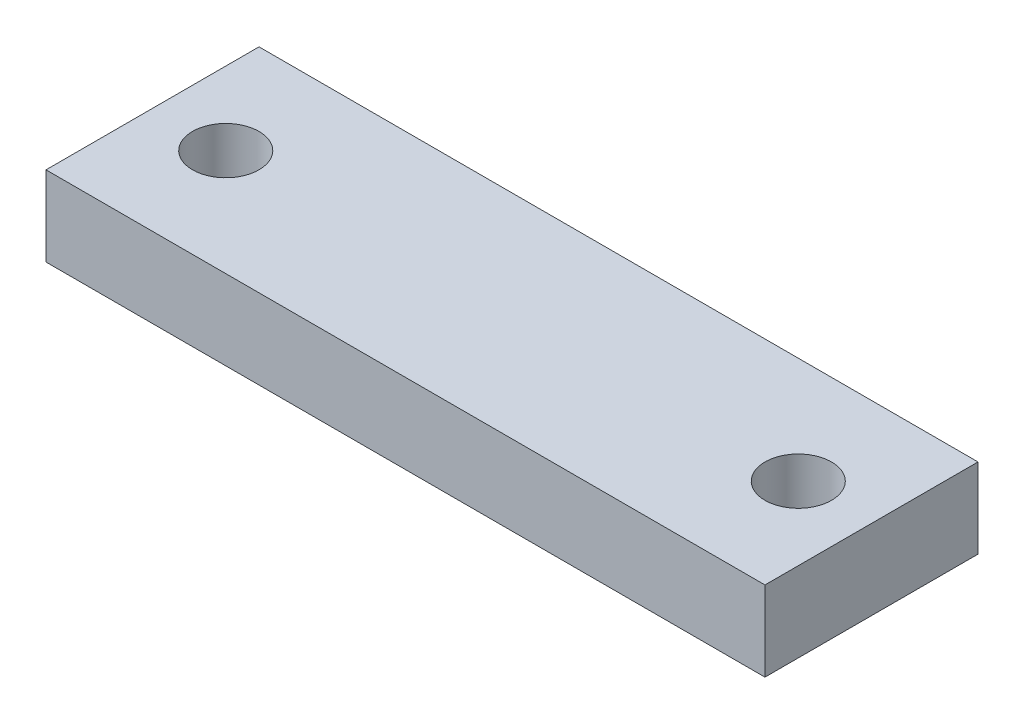
SolidWorks part; units mm, degrees
ref_plane "Front Plane" through (0, 0, 0) normal (0, 0, 1) x (1, 0, 0)
ref_plane "Top Plane" through (0, 0, 0) normal (0, 1, 0) x (1, 0, 0)
ref_plane "Right Plane" through (0, 0, 0) normal (1, 0, 0) x (0, 0, -1)
sketch "Sketch1" plane through (0, 0, 0) normal (0, 1, 0) x (1, 0, 0)
  line L0 (42.8625, 25.4) -> (42.8625, 0) construction
  line L1 (0, 0) -> (85.725, 0)
  line L2 (0, 0) -> (0, 25.4)
  line L3 (0, 25.4) -> (85.725, 25.4)
  line L4 (85.725, 0) -> (85.725, 25.4)
  line L5 (0, 12.7) -> (85.725, 12.7) construction
  circle A0 centre (76.9938, 12.7) radius 3.9687
  circle A1 centre (8.7312, 12.7) radius 3.9687
  dimension "D1" = 68.2625
  dimension "D2" = 34.1313
  dimension "D5" = 7.9375
  dimension "D6" = 7.9375
  dimension "D3" = 85.725
  dimension "D4" = 25.4
extrude "Extrude1" add sketch "Sketch1" along normal blind 9.525
